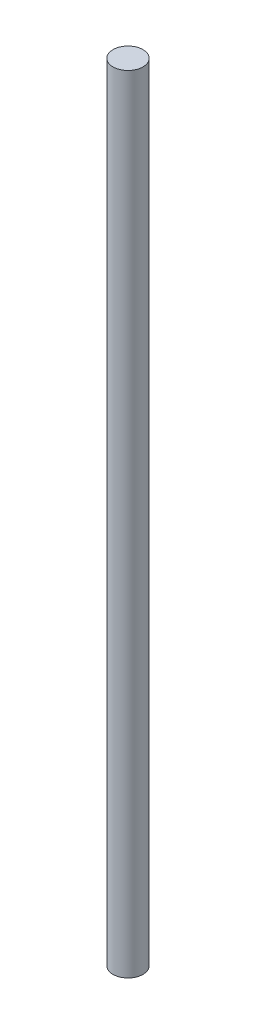
SolidWorks part; units mm, degrees
ref_plane "Front Plane" through (0, 0, 0) normal (0, 0, 1) x (1, 0, 0)
ref_plane "Top Plane" through (0, 0, 0) normal (0, 1, 0) x (1, 0, 0)
ref_plane "Right Plane" through (0, 0, 0) normal (1, 0, 0) x (0, 0, -1)
sketch "Sketch1" plane through (0, 0, 0) normal (0, 1, 0) x (1, 0, 0)
  circle A0 centre (0, 0) radius 5
  dimension "D1" = 10
extrude "Boss-Extrude1" add sketch "Sketch1" along normal blind 262
